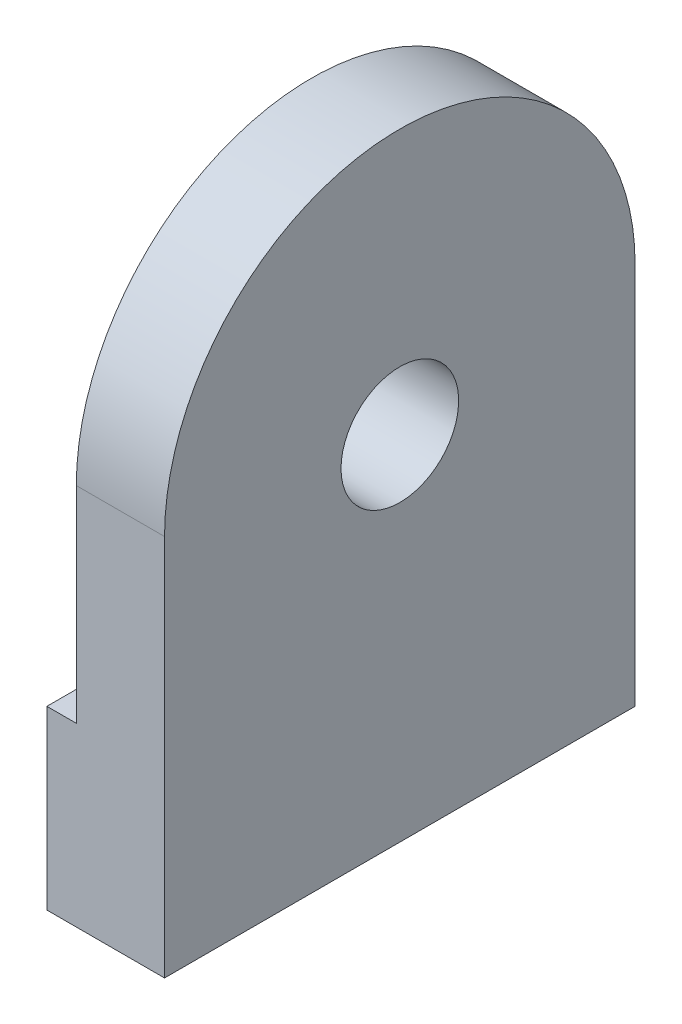
SolidWorks part; units mm, degrees
ref_plane "Front" through (0, 0, 0) normal (0, 0, 1) x (1, 0, 0)
ref_plane "Top" through (0, 0, 0) normal (0, 1, 0) x (1, 0, 0)
ref_plane "Right" through (0, 0, 0) normal (1, 0, 0) x (0, 0, -1)
sketch "Sketch1" plane through (0, 0, 0) normal (1, 0, 0) x (0, 0, -1)
  line L0 (0, 0) -> (0, 6.5)
  line L1 (0, 0) -> (8, 0)
  line L2 (8, 6.5) -> (8, 0)
  line L3 (0, 6.5) -> (8, 6.5) construction
  line L4 (0, 6.5) -> (0, 10.5) construction
  line L5 (0, 10.5) -> (8, 10.5) construction
  line L6 (8, 10.5) -> (8, 6.5) construction
  arc A0 (0, 6.5) -> (8, 6.5) centre (4, 6.5) cw
  dimension "D1" = 8
  dimension "D2" = 10.5
extrude "Boss-Extrude1" add sketch "Sketch1" along normal blind 2
sketch "Sketch2" plane through (0, 0, 0) normal (-1, 0, 0) x (0, 0, 1)
  line L0 (-8, 3) -> (-6, 3)
  line L1 (-8, 0) -> (-8, 6.5) construction
  line L2 (-6, 3) -> (-6, 0)
  line L3 (0, 0) -> (-8, 0) construction
  line L4 (-6, 0) -> (-2, 0)
  line L5 (-2, 0) -> (-2, 3)
  line L6 (-2, 3) -> (0, 3)
  line L7 (0, 6.5) -> (0, 0) construction
  line L8 (0, 3) -> (0, 6.5)
  line L9 (-8, 3) -> (-8, 6.5)
  arc A0 (-8, 6.5) -> (0, 6.5) centre (-4, 6.5) cw
  dimension "D1" = 2
  dimension "D2" = 3
extrude "Cut-Extrude1" cut sketch "Sketch2" against normal blind 0.5
sketch "Sketch3" plane through (0.5, 0, 0) normal (-1, 0, 0) x (0, 0, 1)
  line L0 (-6, 0) -> (-2, 0) construction
  line L1 (-4, 0) -> (-4, 10.5) construction
  circle A0 centre (-4, 6) radius 1
  arc A1 (0, 6.5) -> (-8, 6.5) centre (-4, 6.5) ccw construction
  dimension "D2" = 2
  dimension "D1" = 6
extrude "Cut-Extrude2" cut sketch "Sketch3" against normal through all
